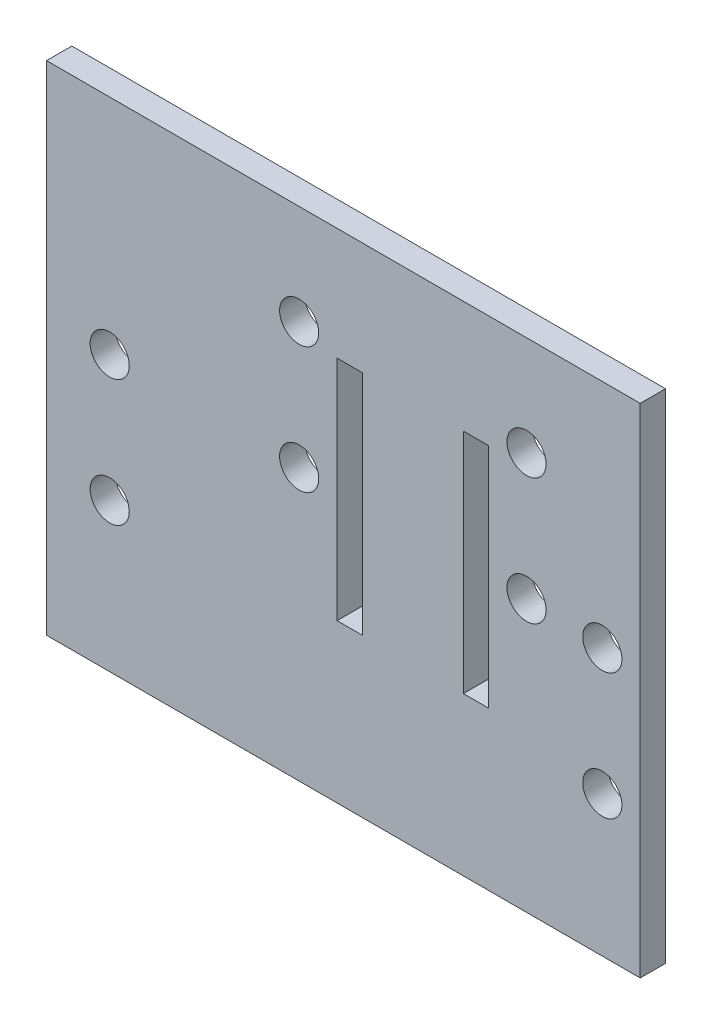
SolidWorks part; units mm, degrees
material "Thornel Mat VMA"
ref_plane "前视基准面" through (0, 0, 0) normal (0, 0, 1) x (1, 0, 0)
ref_plane "上视基准面" through (0, 0, 0) normal (0, 1, 0) x (1, 0, 0)
ref_plane "右视基准面" through (0, 0, 0) normal (1, 0, 0) x (0, 0, -1)
sketch "草图1" plane through (0, 0, 0) normal (0, 0, 1) x (1, 0, 0)
  line L0 (11.5, 10.8) -> (11.5, -7.2)
  line L1 (-23.5, 19.7) -> (23.5, 19.7)
  line L2 (-23.5, 19.7) -> (-23.5, -19.7)
  line L3 (-23.5, -19.7) -> (23.5, -19.7)
  line L4 (23.5, 19.7) -> (23.5, -19.7)
  line L5 (-23.5, 19.7) -> (23.5, -19.7) construction
  line L6 (-23.5, -19.7) -> (23.5, 19.7) construction
  line L7 (11.5, -7.2) -> (9.5, -7.2)
  line L8 (9.5, -7.2) -> (9.5, 10.8)
  line L9 (9.5, 10.8) -> (11.5, 10.8)
  line L10 (-15.1497, 12.7) -> (15.1497, -12.7) construction
  line L11 (1.5, 10.8) -> (1.5, -7.2)
  line L12 (1.5, -7.2) -> (-0.5, -7.2)
  line L13 (-0.5, -7.2) -> (-0.5, 10.8)
  line L14 (-0.5, 10.8) -> (1.5, 10.8)
  circle A0 centre (20.5, 1.43) radius 1.55
  circle A1 centre (20.5, -8.57) radius 1.55
  circle A2 centre (-18.5, 2.05) radius 1.55
  circle A3 centre (-18.5, -7.95) radius 1.55
  circle A4 centre (-3.5, 11.8) radius 1.55
  circle A5 centre (-3.5, 1.8) radius 1.55
  circle A6 centre (14.5, 11.8) radius 1.55
  circle A7 centre (14.5, 1.8) radius 1.55
  point P0 (0, 0)
  point P20 (0, 0)
  dimension "D3" = 3.1
  dimension "D4" = 3.1
  dimension "D5" = 3.1
  dimension "D6" = 3.1
  dimension "D25" = 3.1
  dimension "D26" = 3.1
  dimension "D31" = 3.1
  dimension "D32" = 3.1
  dimension "D1" = 47
  dimension "D2" = 39.4
  dimension "D7" = 11.13
  dimension "D8" = 11.75
  dimension "D9" = 10
  dimension "D10" = 10
  dimension "D11" = 5
  dimension "D12" = 5
  dimension "D13" = 3
  dimension "D14" = 3
  dimension "D15" = 12.5
  dimension "D16" = 18
  dimension "D17" = 2
  dimension "D18" = 12
  dimension "D19" = 7
  dimension "D20" = 7
  dimension "D21" = 2
  dimension "D22" = 8
  dimension "D23" = 12.5
  dimension "D24" = 18
  dimension "D27" = 3
  dimension "D28" = 3
  dimension "D29" = 10
  dimension "D30" = 9
  dimension "D33" = 3
  dimension "D34" = 3
  dimension "D35" = 10
  dimension "D36" = 9
extrude "凸台-拉伸1" add sketch "草图1" along normal blind 2
